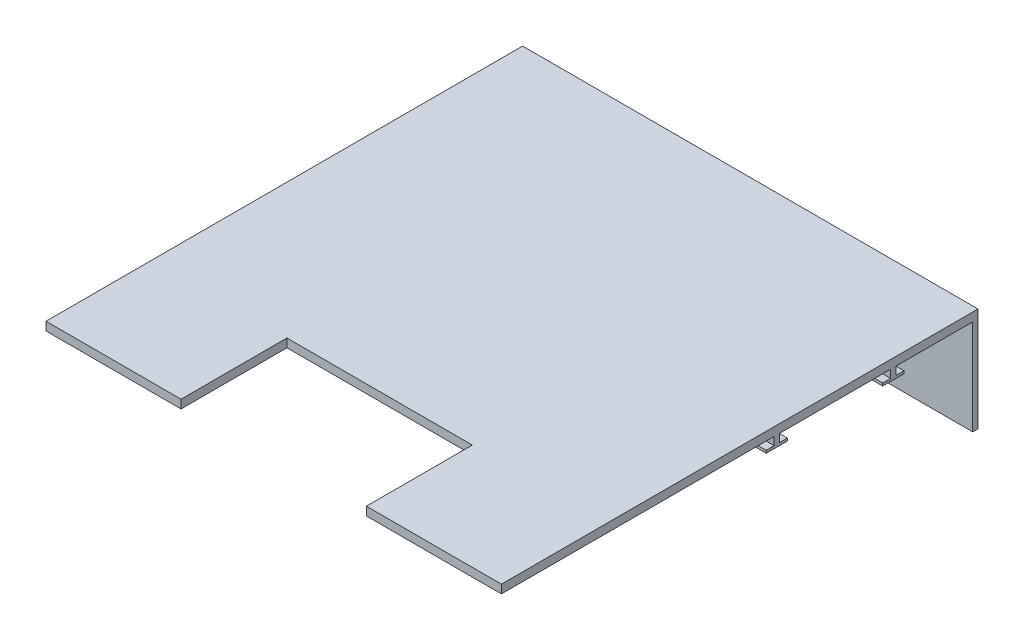
SolidWorks part; units mm, degrees
ref_plane "Front Plane" through (0, 0, 0) normal (0, 0, 1) x (1, 0, 0)
ref_plane "Top Plane" through (0, 0, 0) normal (0, 1, 0) x (1, 0, 0)
ref_plane "Right Plane" through (0, 0, 0) normal (1, 0, 0) x (0, 0, -1)
sketch "Sketch1" plane through (0, 0, 0) normal (0, 1, 0) x (1, 0, 0)
  line L1 (0, 0) -> (430, 0)
  line L2 (0, 0) -> (0, 450)
  line L3 (0, 450) -> (430, 450)
  line L4 (430, 0) -> (430, 450)
  dimension "D1" = 430
  dimension "D2" = 450
extrude "Boss-Extrude1" add sketch "Sketch1" along normal blind 8
sketch "Sketch2" plane through (0, 8, 0) normal (0, 1, 0) x (1, 0, 0)
  line L0 (215, -28.2037) -> (215, 169.1617) construction
  line L2 (127.5, 0) -> (302.5, 0)
  line L3 (127.5, 0) -> (127.5, 100)
  line L4 (127.5, 100) -> (302.5, 100)
  line L5 (302.5, 0) -> (302.5, 100)
  line L6 (0, 0) -> (430, 0) construction
  point P8 (215, 0)
  dimension "D1" = 175
  dimension "D2" = 100
extrude "Cut-Extrude1" cut sketch "Sketch2" against normal blind 10
sketch "Sketch4" plane through (0, 0, 0) normal (0, -1, 0) x (1, 0, 0)
  line L0 (0, -450) -> (0, 0) construction
  line L1 (430, -450) -> (0, -450) construction
  line L2 (215, -100) -> (215, -477.0808) construction
  line L4 (127.5, -100) -> (302.5, -100) construction
  circle A0 centre (30, -217) radius 3.5
  circle A1 centre (400, -217) radius 3.5
  dimension "D1" = 7
  dimension "D2" = 30
  dimension "D3" = 233
extrude "Boss-Extrude3" add sketch "Sketch4" along normal blind 15
sketch "Sketch5" plane through (0, 0, 0) normal (0, -1, 0) x (1, 0, 0)
  line L35 (5.0006, -445) -> (0, -445)
  line L36 (0, -450) -> (0, 0) construction
  line L37 (430, -450) -> (0, -450)
  line L38 (0, -445) -> (0, -450)
  line L39 (429.0083, -445) -> (430, -445)
  line L40 (430, 0) -> (430, -450) construction
  line L41 (430, -445) -> (430, -450)
  line L47 (429.0083, -445) -> (5.0006, -445)
  line L57 (537.7096, -400.1138) -> (429.0083, -445) construction
  line L58 (545.6837, -402.2306) -> (430, -450) construction
  line L59 (338.1864, -135.0174) -> (545.6837, -402.2306) construction
  line L60 (334.2372, -138.084) -> (537.7096, -400.1138) construction
  line L61 (0.0417, -117.3183) -> (152.5, -117.3183) construction
  line L62 (5.041, -122.3183) -> (152.5, -122.3183) construction
  line L63 (5.0006, -445) -> (5.041, -122.3183) construction
  line L64 (0, -450) -> (0.0417, -117.3183) construction
  dimension "D2" = 5
extrude "Boss-Extrude4" add sketch "Sketch5" along normal blind 90
ref_plane "Plane2" through (0, 0, -315) normal (0, 0, 1) x (1, 0, 0)
sketch "Sketch9" plane through (0, 0, 0) normal (0, -1, 0) x (1, 0, 0)
  line L0 (0, -445) -> (0, 0) construction
  line L1 (0, -367.5) -> (430, -367.5)
  line L2 (0, -367.5) -> (0, -372.5)
  line L3 (0, -372.5) -> (430, -372.5)
  line L4 (430, -367.5) -> (430, -372.5)
  line L5 (430, 0) -> (430, -445) construction
  line L7 (0, -370) -> (491.4988, -370) construction
  line L8 (49.5, -315) -> (-49.5, -315) construction
  dimension "D1" = 55
  dimension "D2" = 5
extrude "Boss-Extrude6" add sketch "Sketch9" along normal blind 7.5
sketch "Sketch10" plane through (0, -7.5, 0) normal (0, -1, 0) x (1, 0, 0)
  line L2 (430, -360) -> (0, -360)
  line L3 (430, -360) -> (0, -360)
  line L4 (0, -360) -> (0, -380)
  line L5 (0, -380) -> (430, -380)
  line L6 (0, -380) -> (430, -380)
  line L7 (430, -360) -> (430, -380)
  dimension "D1" = 7.5
  dimension "D2" = 7.5
extrude "Boss-Extrude7" add sketch "Sketch10" along normal blind 2.5
mirror "Mirror9" about plane through (0, 0, -315) normal (0, 0, 1) of "Boss-Extrude6", "Boss-Extrude7"
ref_plane "Plane1" through (240, 0, 0) normal (1, 0, 0) x (0, 0, -1)
